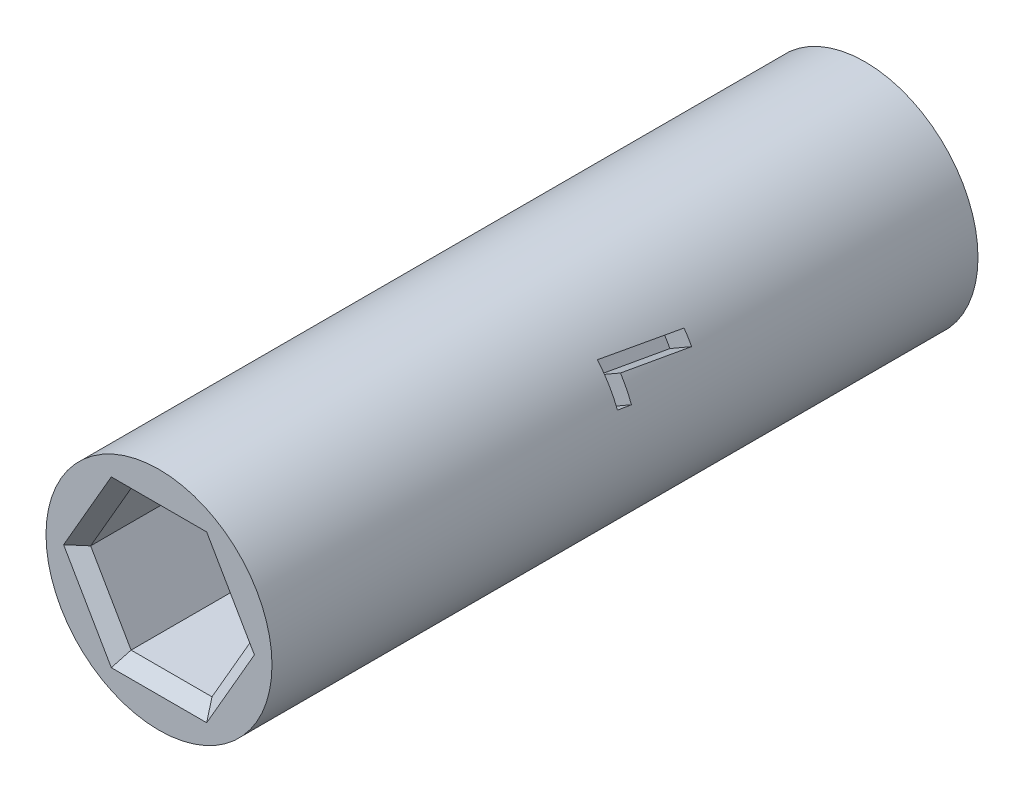
SolidWorks part; units mm, degrees
ref_plane "Front Plane" through (0, 0, 0) normal (0, 0, 1) x (1, 0, 0)
ref_plane "Top Plane" through (0, 0, 0) normal (0, 1, 0) x (1, 0, 0)
ref_plane "Right Plane" through (0, 0, 0) normal (1, 0, 0) x (0, 0, -1)
sketch "Sketch1" plane through (0, 0, 0) normal (0, 1, 0) x (1, 0, 0)
  line L0 (0, 0) -> (0, 63.1171) construction
  line L1 (0, 45.6171) -> (0, 17.5)
  point P3 (0, 39.1171)
  point P4 (0, 24)
  point P5 (0, 45.6171)
  point P6 (0, 17.5)
  dimension "D1" = 63.1171
  dimension "D2" = 24
  dimension "D3" = 24
  dimension "D4" = 15.1171
  dimension "D5" = 6.5
  dimension "D6" = 6.5
revolve "Revolve-Thin1" add sketch "Sketch1" angle 360 about L0 wall 4.5
sketch "Sketch2" plane through (0, 0, -17.5) normal (0, 0, 1) x (1, 0, 0)
  line L1 (1.6108, 2.79) -> (-1.6108, 2.79)
  line L2 (-1.6108, 2.79) -> (-3.2216, 0)
  line L3 (-3.2216, 0) -> (-1.6108, -2.79)
  line L4 (-1.6108, -2.79) -> (1.6108, -2.79)
  line L5 (1.6108, -2.79) -> (3.2216, 0)
  line L6 (3.2216, 0) -> (1.6108, 2.79)
  circle A0 centre (0, 0) radius 2.79 construction
  dimension "D1" = 5.58
extrude "Cut-Extrude1" cut sketch "Sketch2" against normal blind 7
sketch "Sketch3" plane through (0, 0, -45.6171) normal (0, 0, -1) x (-1, 0, 0)
  line L1 (1.6108, 2.79) -> (-1.6108, 2.79)
  line L2 (-1.6108, 2.79) -> (-3.2216, 0)
  line L3 (-3.2216, 0) -> (-1.6108, -2.79)
  line L4 (-1.6108, -2.79) -> (1.6108, -2.79)
  line L5 (1.6108, -2.79) -> (3.2216, 0)
  line L6 (3.2216, 0) -> (1.6108, 2.79)
  circle A0 centre (0, 0) radius 2.79 construction
  dimension "D1" = 5.58
extrude "Cut-Extrude2" cut sketch "Sketch3" against normal blind 7
chamfer "Chamfer1" distance 0.5 angle 45 12 edges at (2.4162, 1.395, -17.5) (2.4162, -1.395, -17.5) (0, -2.79, -17.5) (-2.4162, -1.395, -17.5) (-2.4162, 1.395, -17.5) (0, 2.79, -17.5) (0, 2.79, -45.6171) (-2.4162, 1.395, -45.6171) (-2.4162, -1.395, -45.6171) (0, -2.79, -45.6171) (2.4162, -1.395, -45.6171) (2.4162, 1.395, -45.6171)
sketch3d "3DSketch1" plane through (0, 0, 0) normal (0, 0, 1) x (1, 0, 0)
sketch "Sketch4" plane through (3.8971, 2.25, 0) normal (0.866, 0.5, 0) x (0, 0, -1)
  line L0 (45.6171, -4.5) -> (45.6171, 4.5) construction
  line L1 (45.6171, -4.5) -> (45.6171, 4.5) construction
  line L2 (0, 0) -> (45.6171, 0) construction
  line L3 (17.5, 4.5) -> (17.5, -4.5) construction
  line L4 (17.5, 4.5) -> (17.5, -4.5) construction
  line L5 (17.5, 4.5) -> (45.6171, 4.5) construction
  line L6 (31.5585, 4.5) -> (31.5585, -4.5) construction
  line L7 (17.5, -4.5) -> (45.6171, -4.5) construction
  text T0 "<b><i>L</i></b>"
extrude "Cut-Extrude3" cut sketch "Sketch4" against normal blind 1
